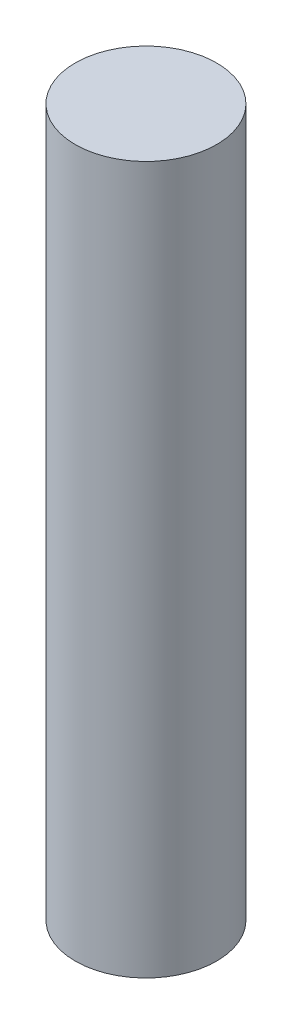
SolidWorks part; units mm, degrees
ref_plane "Front Plane" through (0, 0, 0) normal (0, 0, 1) x (1, 0, 0)
ref_plane "Top Plane" through (0, 0, 0) normal (0, 1, 0) x (1, 0, 0)
ref_plane "Right Plane" through (0, 0, 0) normal (1, 0, 0) x (0, 0, -1)
sketch "Sketch1" plane through (0, 0, 0) normal (0, 1, 0) x (1, 0, 0)
  circle A0 centre (0, 0) radius 3.2
  dimension "D1" = 6.4
extrude "Boss-Extrude1" add sketch "Sketch1" along normal blind 32
